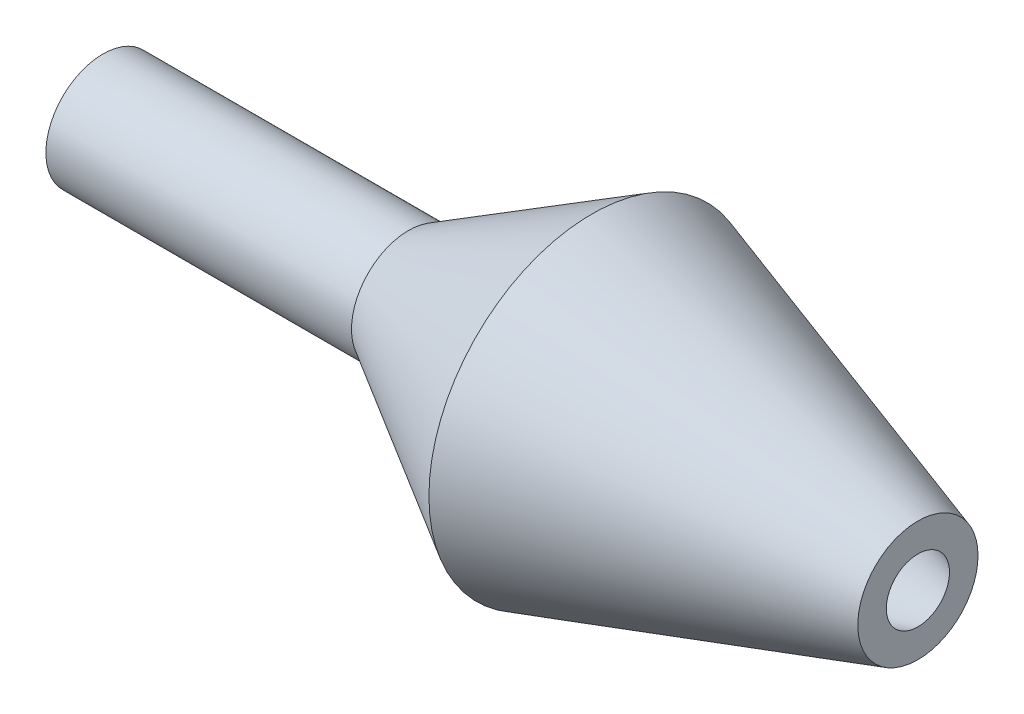
SolidWorks part; units mm, degrees
ref_plane "Front Plane" through (0, 0, 0) normal (0, 0, 1) x (1, 0, 0)
ref_plane "Top Plane" through (0, 0, 0) normal (0, 1, 0) x (1, 0, 0)
ref_plane "Right Plane" through (0, 0, 0) normal (1, 0, 0) x (0, 0, -1)
sketch "Sketch1" plane through (0, 0, 0) normal (0, 1, 0) x (1, 0, 0)
  line L0 (0, 0) -> (-40, 0) construction
  line L1 (-40, 1.4) -> (-25, 1.4)
  line L3 (-16, 8) -> (0, 2.95)
  line L4 (-40, 2.8) -> (-25, 2.8)
  line L5 (-25, 2.8) -> (-16, 8)
  line L6 (0, 1.55) -> (-16, 6.6)
  line L7 (-16, 6.6) -> (-25, 1.4)
  line L9 (-40, 2.8) -> (-40, 1.4)
  line L10 (0, 2.95) -> (0, 1.55)
  point P11 (0, 0)
  point P12 (0, 0)
  point P13 (0, 0)
  point P14 (0, 0)
  point P15 (-38.8723, 1.4)
  point P16 (0, 0)
  dimension "D1" = 40
  dimension "D3" = 1.4
  dimension "D4" = 2.95
  dimension "D5" = 8
  dimension "D6" = 1.4
  dimension "D7" = 1.4
  dimension "D8" = 1.4
  dimension "D9" = 15
  dimension "D10" = 16
revolve "Revolve1" add sketch "Sketch1" angle 360 about L0
